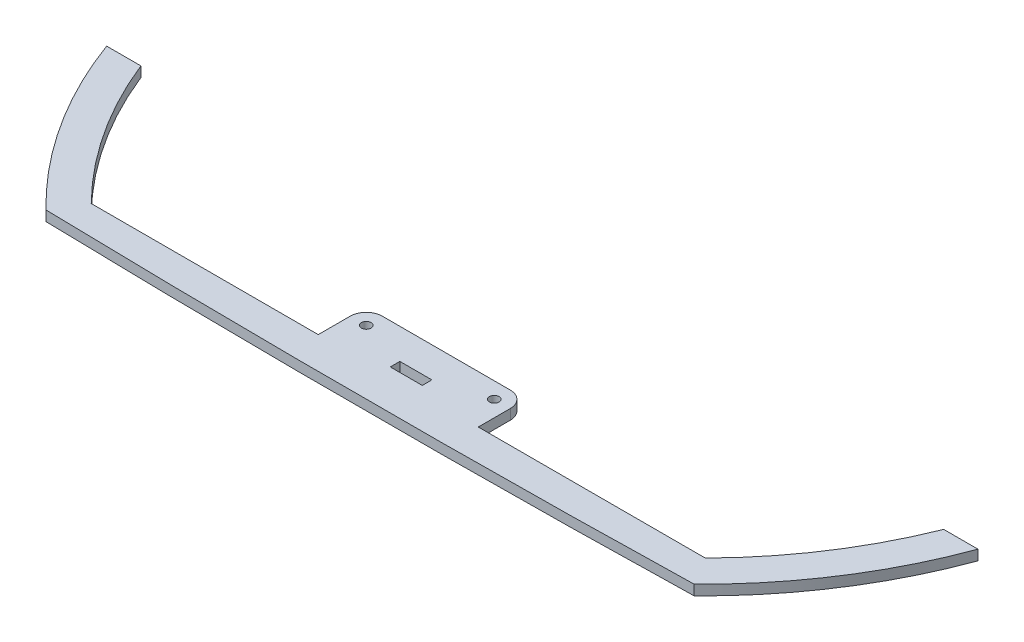
SolidWorks part; units mm, degrees
ref_plane "前视基准面" through (0, 0, 0) normal (0, 0, 1) x (1, 0, 0)
ref_plane "上视基准面" through (0, 0, 0) normal (0, 1, 0) x (1, 0, 0)
ref_plane "右视基准面" through (0, 0, 0) normal (1, 0, 0) x (0, 0, -1)
other "Configuration Table"
sketch "草图1" plane through (0, 0, 0) normal (0, 1, 0) x (1, 0, 0)
  line L0 (0, 0) -> (34.1522, 0) construction
  line L5 (-25, -10) -> (-95.9166, -10)
  line L6 (-20, 5) -> (20, 5)
  line L7 (0, 0) -> (0, 15.8828) construction
  line L8 (-25, 0) -> (-25, -10)
  line L10 (25, 0) -> (25, -10)
  line L11 (25, -10) -> (95.9166, -10)
  line L12 (-136.1066, 35) -> (-125.3994, 35)
  line L13 (125.3994, 35) -> (136.1066, 35)
  line L15 (-5, -4.5) -> (5, -4.5)
  line L16 (-5, -4.5) -> (-5, -7.5)
  line L17 (-5, -7.5) -> (5, -7.5)
  line L18 (5, -4.5) -> (5, -7.5)
  line L19 (-5, -4.5) -> (5, -7.5) construction
  line L20 (-5, -7.5) -> (5, -4.5) construction
  circle A0 centre (-20, 0) radius 1.5
  circle A1 centre (20, 0) radius 1.5
  arc A2 (20, 5) -> (25, 0) centre (20, 0) cw
  arc A3 (-20, 5) -> (-25, 0) centre (-20, 0) ccw
  arc A5 (101.2484, -18.7967) -> (136.1066, 35) centre (0, 85) ccw
  arc A6 (95.9166, -10) -> (125.3994, 35) centre (0, 85) ccw
  arc A7 (-136.1066, 35) -> (-101.2484, -18.7967) centre (0, 85) ccw
  arc A8 (-125.3994, 35) -> (-95.9166, -10) centre (0, 85) ccw
  ellipse E0 centre (0, -10) end of major axis (-212.8934, -10) minor radius 10 (-101.2484, -18.7967) -> (101.2484, -18.7967) ccw
  point P0 (0, 0)
  point P14 (0, -6)
  point P24 (25, 5)
  point P30 (0, 85)
  dimension "D1" = 3
  dimension "D3" = 5
  dimension "D10" = 290
  dimension "D11" = 270
  dimension "D2" = 40
  dimension "D4" = 25
  dimension "D5" = 5
  dimension "D6" = 15
  dimension "D7" = 10
  dimension "D8" = 3
  dimension "D9" = 20
  dimension "D12" = 45
  dimension "D13" = 6
extrude "凸台-拉伸1" add sketch "草图1" along normal blind 3.175
